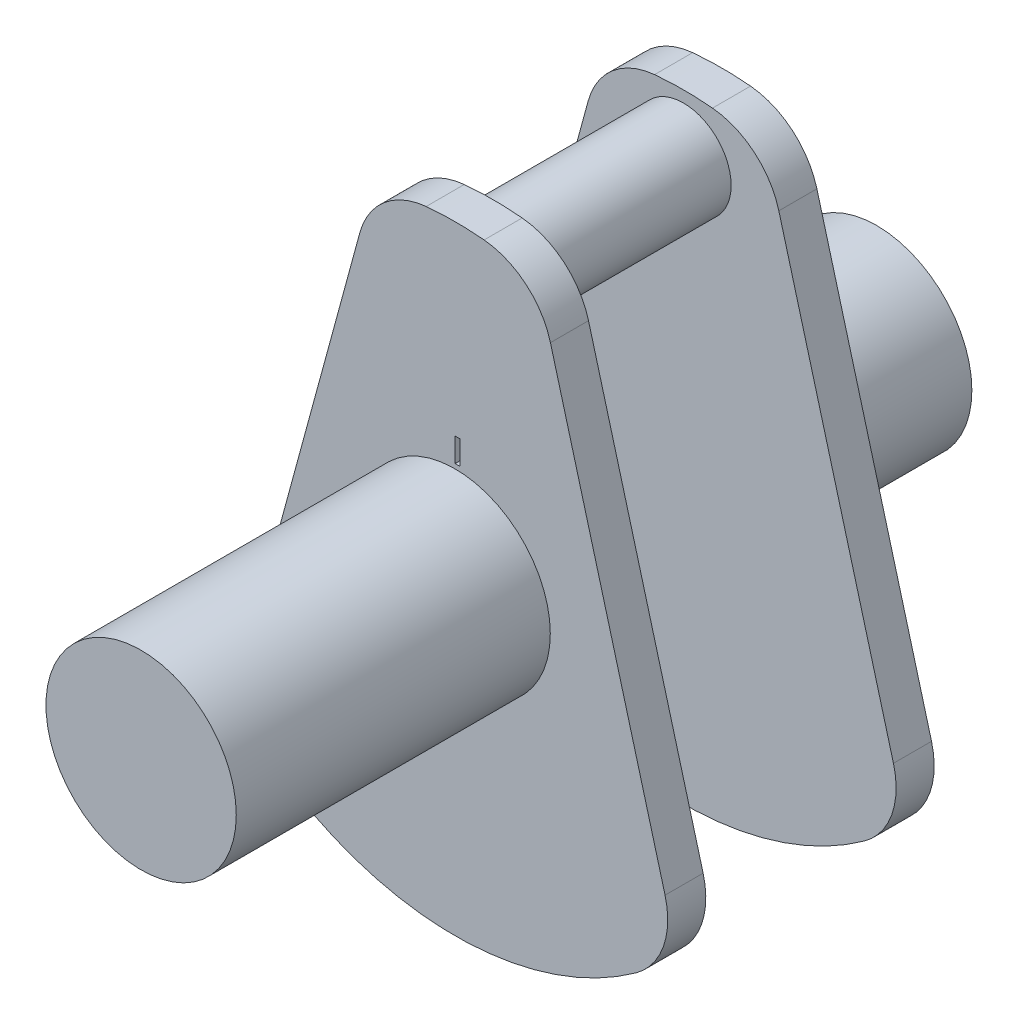
SolidWorks part; units mm, degrees
ref_plane "Front Plane" through (0, 0, 0) normal (0, 0, 1) x (1, 0, 0)
ref_plane "Top Plane" through (0, 0, 0) normal (0, 1, 0) x (1, 0, 0)
ref_plane "Right Plane" through (0, 0, 0) normal (1, 0, 0) x (0, 0, -1)
sketch "Sketch1" plane through (0, 0, 0) normal (0, 0, 1) x (1, 0, 0)
  line L0 (0, 65) -> (0, -65) construction
  line L1 (-20.0284, 52.9863) -> (-44.1187, -35.5279)
  line L2 (20.0284, 52.9863) -> (44.1187, -35.5279)
  arc A0 (-38.0452, -52.7026) -> (38.0452, -52.7026) centre (0, 0) ccw
  arc A1 (6.0888, 64.7142) -> (-6.0888, 64.7142) centre (0, 0) ccw
  arc A2 (20.0284, 52.9863) -> (6.0888, 64.7142) centre (4.59, 48.7845) ccw
  arc A3 (-20.0284, 52.9863) -> (-6.0888, 64.7142) centre (-4.59, 48.7845) cw
  arc A4 (44.1187, -35.5279) -> (38.0452, -52.7026) centre (28.6802, -39.7296) cw
  arc A5 (-44.1187, -35.5279) -> (-38.0452, -52.7026) centre (-28.6802, -39.7296) ccw
  point P12 (17.4047, 62.6265)
  point P15 (-17.4047, 62.6265)
  point P18 (46.7424, -45.168)
  point P21 (-46.7424, -45.168)
  dimension "D1" = 130
  dimension "D4" = 16
  dimension "D5" = 16
  dimension "D2" = 30.45
  dimension "D3" = 9.18
extrude "Boss-Extrude1" add sketch "Sketch1" along normal blind 8
sketch "Sketch2" plane through (0, 0, 8) normal (0, 0, 1) x (1, 0, 0)
  line L0 (0, 65) -> (0, 52.59) construction
  arc A0 (6.0888, 64.7142) -> (-6.0888, 64.7142) centre (0, 0) ccw construction
  circle A1 centre (0, 52.59) radius 10
  dimension "D1" = 20
  dimension "D2" = 52.59
extrude "Boss-Extrude2" add sketch "Sketch2" along normal blind 20
sketch "Sketch3" plane through (0, 0, 0) normal (0, 0, -1) x (-1, 0, 0)
  circle A0 centre (0, 0) radius 20
  dimension "D1" = 40
extrude "Boss-Extrude3" add sketch "Sketch3" along normal blind 32.6
mirror "Mirror1" about plane through (0, 52.59, 28) normal (0, 0, 1) of bodies 103
sketch "Sketch4" plane through (0, 0, 88.6) normal (0, 0, 1) x (1, 0, 0)
  circle A1 centre (0, 0) radius 20
  circle A2 centre (0, 0) radius 20
  dimension "D1" = 0
extrude "Boss-Extrude4" add sketch "Sketch4" along normal blind 33.4
scale "Scale1" bodies to scale 105 scale about centroid uniform scaling yes scale factor 0.1
sketch "Sketch5" plane through (0, 0, 41.725) normal (0, 0, 1) x (1, 0, 0)
  line L0 (0, 0) -> (0, 3.209) construction
  line L2 (0, 1.5017) -> (0.1, 1.5017)
  line L3 (0, 1.5017) -> (0, 1.0017)
  line L4 (0, 1.0017) -> (0.1, 1.0017)
  line L5 (0.1, 1.5017) -> (0.1, 1.0017)
  point P7 (0, 1.0017)
  dimension "D1" = 0.1
  dimension "D2" = 0.5
extrude "Cut-Extrude1" cut sketch "Sketch5" against normal blind 0.1
